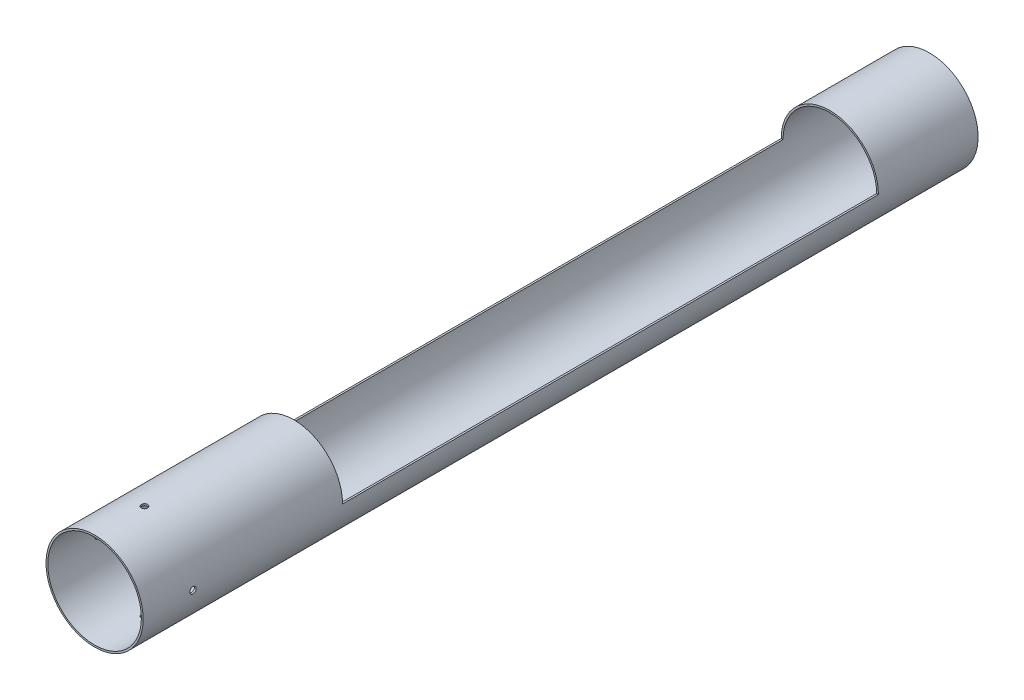
SolidWorks part; units mm, degrees
ref_plane "Front Plane" through (0, 0, 0) normal (0, 0, 1) x (1, 0, 0)
ref_plane "Top Plane" through (0, 0, 0) normal (0, 1, 0) x (1, 0, 0)
ref_plane "Right Plane" through (0, 0, 0) normal (1, 0, 0) x (0, 0, -1)
sketch "Sketch1" plane through (0, 0, 0) normal (0, 0, 1) x (1, 0, 0)
  line L0 (-49.5046, 0) -> (-47.6885, 0)
  line L1 (47.6885, 0) -> (49.5046, 0)
  arc A0 (-49.5046, 0) -> (49.5046, 0) centre (0, 0) ccw
  arc A1 (-47.6885, 0) -> (47.6885, 0) centre (0, 0) ccw
  dimension "D1" = 95.377
  dimension "D2" = 99.0092
extrude "Boss-Extrude1" add sketch "Sketch1" along normal blind 546.1
sketch "Sketch2" plane through (0, 0, 546.1) normal (0, 0, 1) x (1, 0, 0)
  circle A0 centre (0, 0) radius 47.6885
  circle A1 centre (0, 0) radius 49.5046
  arc A2 (-47.6885, 0) -> (47.6885, 0) centre (0, 0) ccw construction
  arc A3 (-49.5046, 0) -> (49.5046, 0) centre (0, 0) ccw construction
extrude "Boss-Extrude2" add sketch "Sketch2" along normal blind 203.2
sketch "Sketch3" plane through (0, 0, 0) normal (0, 0, -1) x (-1, 0, 0)
  circle A0 centre (0, 0) radius 47.6885
  circle A1 centre (0, 0) radius 49.5046
  arc A2 (-47.6885, 0) -> (47.6885, 0) centre (0, 0) ccw construction
  arc A3 (-49.5046, 0) -> (49.5046, 0) centre (0, 0) ccw construction
extrude "Boss-Extrude3" add sketch "Sketch3" along normal blind 101.6
sketch "Sketch4" plane through (0, 0, 0) normal (0, 1, 0) x (1, 0, 0)
  line L0 (-49.5046, -749.3) -> (49.5046, -749.3) construction
  line L1 (-49.5046, -749.3) -> (49.5046, -749.3) construction
  circle A0 centre (0, -698.5) radius 3.175
  point P4 (0, -749.3)
  dimension "D1" = 6.35
  dimension "D2" = 50.8
extrude "Cut-Extrude1" cut sketch "Sketch4" against normal through all
pattern_circular "CirPattern1" count 4 over 360 about axis through (0, 0, 546.1) along (0, 0, -1) of "Cut-Extrude1"
